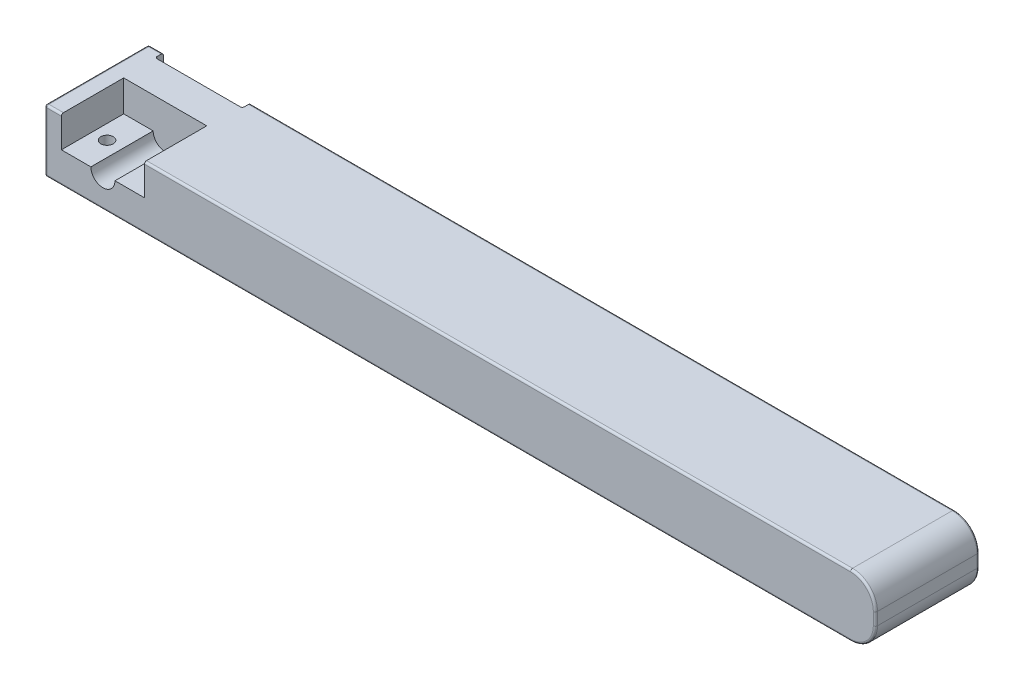
SolidWorks part; units mm, degrees
ref_plane "Ön Düzlem" through (0, 0, 0) normal (0, 0, 1) x (1, 0, 0)
ref_plane "Üst Düzlem" through (0, 0, 0) normal (0, 1, 0) x (1, 0, 0)
ref_plane "Sağ Düzlem" through (0, 0, 0) normal (1, 0, 0) x (0, 0, -1)
sketch "Çizim1" plane through (0, 0, 0) normal (0, 0, 1) x (1, 0, 0)
  line L1 (10.6103, -4.9531) -> (-189.3897, -4.9531)
  line L2 (10.6103, -4.9531) -> (10.6103, 10.0469)
  line L3 (10.6103, 10.0469) -> (-189.3897, 10.0469)
  line L4 (-189.3897, -4.9531) -> (-189.3897, 10.0469)
  dimension "D1" = 200
  dimension "D2" = 15
extrude "Yükseklik-Ekstrüzyon1" add sketch "Çizim1" along normal blind 25
fillet "Radyus1" radius 6 2 edges at (10.6103, -4.9531, 12.5) (10.6103, 10.0469, 12.5)
sketch "Çizim3" plane through (0, 0, 25) normal (0, 0, 1) x (1, 0, 0)
  line L0 (4.6103, 10.0469) -> (-189.3897, 10.0469) construction
  line L1 (-189.3897, 10.0469) -> (-189.3897, -4.9531) construction
  circle A0 centre (-175.3897, 2.5469) radius 2.9
  dimension "D2" = 5.8
  dimension "D1" = 7.5
  dimension "D3" = 14
extrude "Kes-Ekstrüzyon2" cut sketch "Çizim3" against normal blind 15 and the other way through all
sketch "Çizim4" plane through (0, 0, 0) normal (0, 0, -1) x (-1, 0, 0)
  line L1 (175.3897, 2.5469) -> (183.1397, 2.5469)
  line L2 (175.3897, 2.5469) -> (175.3897, -2.0831)
  line L3 (175.3897, -2.0831) -> (183.1397, -2.0831)
  line L4 (183.1397, 2.5469) -> (183.1397, -2.0831)
  line L5 (175.3897, -2.0831) -> (167.6397, -2.0831)
  line L6 (175.3897, -2.0831) -> (175.3897, 2.5469)
  line L7 (175.3897, 2.5469) -> (167.6397, 2.5469)
  line L8 (167.6397, -2.0831) -> (167.6397, 2.5469)
  circle A0 centre (183.1397, -2.0831) radius 1.45
  circle A1 centre (167.6397, -2.0831) radius 1.45
  dimension "D4" = 2.9
  dimension "D5" = 2.9
  dimension "D1" = 7.75
  dimension "D2" = 4.63
  dimension "D3" = 7.75
extrude "Kes-Ekstrüzyon3" cut sketch "Çizim4" against normal blind 10 contours L5 A1 L8 | L8 A1 L5 | L4 A0 L3 | L3 A0 L4
sketch "Çizim6" plane through (0, 0, 0) normal (0, 0, -1) x (-1, 0, 0)
  line L0 (183.1397, -2.0831) -> (185.8397, -2.0831)
  line L4 (185.8397, 10.0469) -> (165.2388, 10.0469)
  line L6 (-4.6103, 10.0469) -> (189.3897, 10.0469) construction
  line L7 (189.3897, -4.9531) -> (-4.6103, -4.9531) construction
  line L8 (185.8397, -4.9531) -> (164.8397, -4.9531)
  line L9 (185.8397, -4.9531) -> (185.8397, 10.0469)
  line L10 (185.8397, 10.0469) -> (164.8397, 10.0469)
  line L11 (164.8397, -4.9531) -> (164.8397, 10.0469)
  dimension "D1" = 2.7
  dimension "D2" = 21
extrude "Kes-Ekstrüzyon4" cut sketch "Çizim6" against normal blind 2
sketch "Çizim8" plane through (0, 0, 25) normal (0, 0, 1) x (1, 0, 0)
  line L0 (4.6103, 10.0469) -> (-189.3897, 10.0469) construction
  line L1 (-185.3897, 10.0469) -> (-165.3897, 10.0469)
  line L2 (-185.3897, 10.0469) -> (-185.3897, 2.5469)
  line L3 (-185.3897, 2.5469) -> (-165.3897, 2.5469)
  line L4 (-165.3897, 10.0469) -> (-165.3897, 2.5469)
  line L5 (-189.3897, 10.0469) -> (-189.3897, -4.9531) construction
  dimension "D1" = 7.5
  dimension "D2" = 4
  dimension "D3" = 20
extrude "Kes-Ekstrüzyon6" cut sketch "Çizim8" against normal blind 15
sketch "Çizim9" plane through (0, 2.5469, 0) normal (0, 1, 0) x (1, 0, 0)
  line L0 (-165.3897, -10) -> (-165.3897, -25) construction
  line L1 (-172.4897, -25) -> (-165.3897, -25) construction
  line L2 (-185.3897, -25) -> (-178.2897, -25) construction
  circle A0 centre (-168.8897, -17.5) radius 1.5
  circle A1 centre (-181.8897, -17.5) radius 1.5
  point P8 (0, 0)
  dimension "D3" = 3
  dimension "D4" = 3
  dimension "D1" = 3.5
  dimension "D2" = 7.5
  dimension "D5" = 7.5
  dimension "D6" = 3.5
extrude "Kes-Ekstrüzyon7" cut sketch "Çizim9" against normal blind 15
fillet "Radyus2" radius 0.5 19 edges at (8.853, -3.1957, 0) (10.6103, 2.5469, 0) (8.853, 8.2896, 0) (8.853, 8.2896, 25) (10.6103, 2.5469, 25) (8.853, -3.1957, 25) (-185.8397, 2.5469, 2) (-164.8397, 2.5469, 2) (-189.3897, 2.5469, 25) (-189.3897, -4.9531, 12.5) (-189.3897, 2.5469, 0) (-189.3897, 10.0469, 12.5) (-80.1147, -4.9531, 0) (-80.1147, 10.0469, 0) (-80.3897, 10.0469, 25) (-92.3897, -4.9531, 25) (-187.6147, -4.9531, 0) (-187.6147, 10.0469, 0) (-187.3897, 10.0469, 25)
